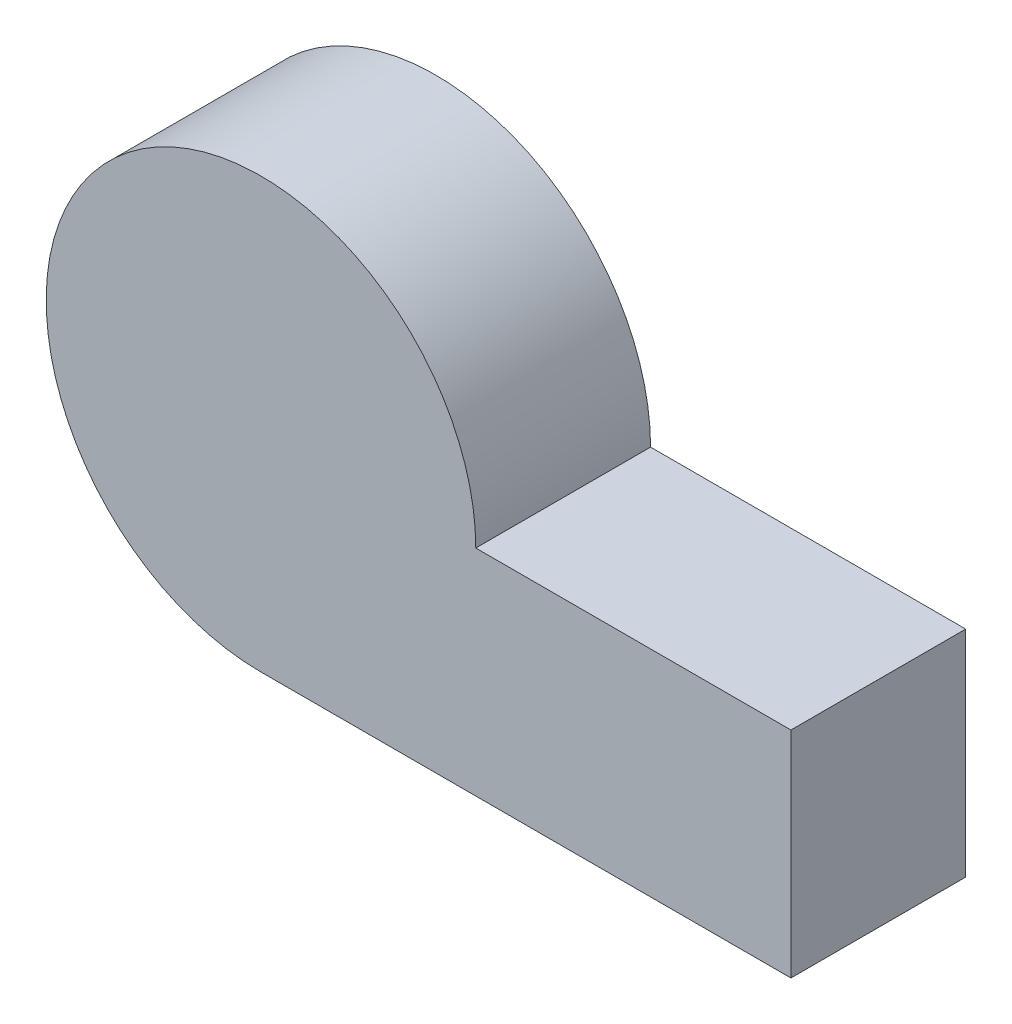
SolidWorks part; units mm, degrees
ref_plane "正面" through (0, 0, 0) normal (0, 0, 1) x (1, 0, 0)
ref_plane "平面" through (0, 0, 0) normal (0, 1, 0) x (1, 0, 0)
ref_plane "右側面" through (0, 0, 0) normal (1, 0, 0) x (0, 0, -1)
sketch "ｽｹｯﾁ1" plane through (0, 0, 0) normal (0, 0, 1) x (1, 0, 0)
  line L1 (0, 0) -> (81.8616, 0)
  line L3 (33.1795, 33.1795) -> (81.8616, 33.1795)
  line L4 (81.8616, 0) -> (81.8616, 33.1795)
  arc A0 (33.1795, 33.1795) -> (0, 0) centre (0, 33.1795) ccw
extrude "ﾎﾞｽ - 押し出し2" add sketch "ｽｹｯﾁ1" along normal blind 27
